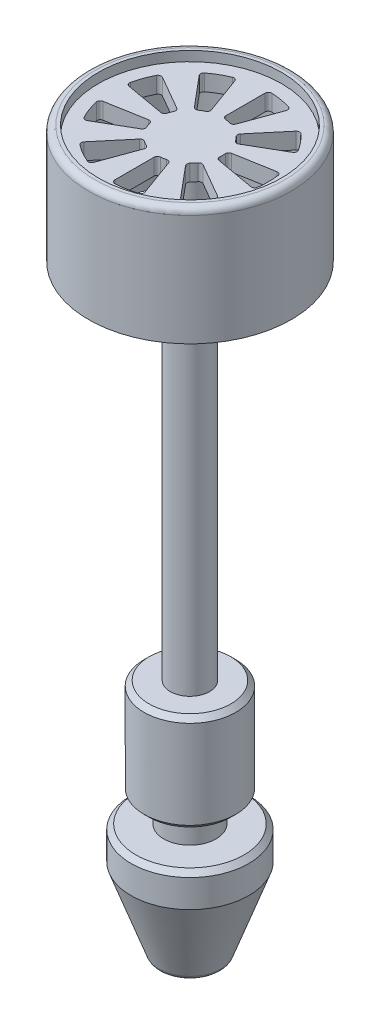
SolidWorks part; units mm, degrees
ref_plane "Alzado" through (0, 0, 0) normal (0, 0, 1) x (1, 0, 0)
ref_plane "Planta" through (0, 0, 0) normal (0, 1, 0) x (1, 0, 0)
ref_plane "Vista lateral" through (0, 0, 0) normal (1, 0, 0) x (0, 0, -1)
sketch "Croquis1" plane through (0, 0, 0) normal (0, 0, 1) x (1, 0, 0)
  line L0 (0, 0) -> (207.3621, 0) construction
  line L1 (0, 120) -> (239.3496, 120) construction
  line L2 (103.6811, 0) -> (103.6811, 171.5103) construction
  line L3 (97.6811, 120) -> (97.6811, 0)
  line L4 (97.6811, 0) -> (97.6811, -3.9826)
  line L5 (95.6811, -41.9826) -> (85.6811, -41.9826)
  line L6 (85.6811, -41.9826) -> (85.6811, -51.9826)
  line L7 (85.6811, -51.9826) -> (94.6811, -76.9826)
  line L8 (94.6811, -76.9826) -> (97.6811, -76.9826)
  line L9 (97.6811, -76.9826) -> (97.6811, -60.9826)
  line L10 (97.6811, -60.9826) -> (103.6811, -60.9826)
  line L11 (97.6811, 120) -> (97.6811, 135)
  line L12 (97.6811, 135) -> (75.6811, 135)
  line L13 (75.6811, 135) -> (75.6811, 107)
  line L14 (75.6811, 107) -> (72.6811, 107)
  line L15 (72.6811, 107) -> (72.6811, 143)
  line L16 (72.6811, 143) -> (75.6811, 143)
  line L17 (75.6811, 143) -> (75.6811, 140)
  line L18 (75.6811, 140) -> (103.6811, 140)
  line L19 (97.6811, -3.9826) -> (89.6811, -3.9826)
  line L20 (89.6811, -3.9826) -> (89.6811, -33.9826)
  line L21 (89.6811, -33.9826) -> (95.6811, -33.9826)
  line L22 (95.6811, -33.9826) -> (95.6811, -41.9826)
  line L23 (103.6811, -60.9826) -> (103.6811, 140)
  dimension "D4" = 56
  dimension "D10" = 14
  dimension "D1" = 120
  dimension "D2" = 12
  dimension "D3" = 207.3621
  dimension "D5" = 15
  dimension "D6" = 5
  dimension "D7" = 3
  dimension "D8" = 3
  dimension "D9" = 36
  dimension "D11" = 30
  dimension "D12" = 3.9826
  dimension "D13" = 8
  dimension "D14" = 18
  dimension "D15" = 10
  dimension "D16" = 8
  dimension "D17" = 35
  dimension "D18" = 16
  dimension "D19" = 6
  dimension "D20" = 3
revolve "Revolución1" add sketch "Croquis1" angle 360 about L23
fillet "Redondeo1" radius 2 1 edges at (103.6811, 143, -31)
chamfer "Chaflán1" distance 1.5 angle 45 3 edges at (103.6811, -41.9826, -18) (103.6811, -33.9826, -14) (103.6811, -3.9826, -14)
fillet "Redondeo2" radius 2 1 edges at (103.6811, -76.9826, -9)
sketch "Croquis2" plane through (0, 140, 0) normal (0, 1, 0) x (1, 0, 0)
  line L0 (103.6811, 10.9545) -> (103.6811, 22.9783)
  line L1 (107.4277, 10.2938) -> (111.5401, 21.5925)
  line L2 (110.7224, 8.3916) -> (118.4512, 17.6024)
  line L3 (113.1679, 5.4772) -> (123.5808, 11.4891)
  line L4 (114.4691, 1.9022) -> (126.3102, 3.9901)
  line L5 (114.4691, -1.9022) -> (126.3102, -3.9901)
  line L6 (113.1679, -5.4772) -> (123.5808, -11.4891)
  line L7 (110.7224, -8.3916) -> (118.4512, -17.6024)
  line L9 (103.6811, -10.9545) -> (103.6811, -22.9783)
  line L10 (99.9344, -10.2938) -> (95.822, -21.5925)
  line L11 (96.6397, -8.3916) -> (88.9109, -17.6024)
  line L12 (94.1942, -5.4772) -> (83.7813, -11.4891)
  line L13 (92.893, -1.9022) -> (81.0519, -3.9901)
  line L14 (92.893, 1.9022) -> (81.0519, 3.9901)
  line L15 (94.1942, 5.4772) -> (83.7813, 11.4891)
  line L16 (96.6397, 8.3916) -> (88.9109, 17.6024)
  line L17 (99.9344, 10.2938) -> (95.822, 21.5925)
  line L18 (107.4277, -10.2938) -> (111.5401, -21.5925)
  line L19 (100.2609, 9.3969) -> (103.6811, 0) [skipped]
  arc A0 (106.2328, 9.6689) -> (104.5902, 9.9586) centre (103.6811, 0) ccw
  arc A1 (110.9012, 22.8882) -> (104.7245, 23.9773) centre (103.6811, 0) ccw
  circle A2 centre (103.6811, 0) radius 24
  arc A3 (94.4998, 22.1744) -> (89.0681, 19.0384) centre (103.6811, 0) ccw
  arc A4 (111.8509, 5.7666) -> (110.7787, 7.0444) centre (103.6811, 0) ccw
  circle A5 centre (103.6811, 0) radius 10
  arc A6 (99.4208, 9.0471) -> (97.9762, 8.2131) centre (103.6811, 0) ccw
  arc A7 (123.9243, 12.8923) -> (119.8927, 17.6969) centre (103.6811, 0) ccw
  arc A8 (113.6462, -0.834) -> (113.6462, 0.834) centre (103.6811, 0) ccw
  arc A9 (127.4753, -3.136) -> (127.4753, 3.136) centre (103.6811, 0) ccw
  arc A10 (110.7787, -7.0444) -> (111.8509, -5.7666) centre (103.6811, 0) ccw
  arc A11 (119.8927, -17.6969) -> (123.9243, -12.8923) centre (103.6811, 0) ccw
  arc A12 (104.5902, -9.9586) -> (106.2328, -9.6689) centre (103.6811, 0) ccw
  arc A13 (104.7245, -23.9773) -> (110.9012, -22.8882) centre (103.6811, 0) ccw
  arc A14 (97.9762, -8.2131) -> (99.4208, -9.0471) centre (103.6811, 0) ccw
  arc A15 (89.0681, -19.0384) -> (94.4998, -22.1744) centre (103.6811, 0) ccw
  arc A16 (94.0316, -2.6246) -> (94.6021, -4.192) centre (103.6811, 0) ccw
  arc A17 (80.2492, -5.1912) -> (82.3944, -11.085) centre (103.6811, 0) ccw
  arc A18 (94.6021, 4.192) -> (94.0316, 2.6246) centre (103.6811, 0) ccw
  arc A19 (82.3944, 11.085) -> (80.2492, 5.1912) centre (103.6811, 0) ccw
  arc A20 (83.7813, 11.4891) -> (82.3944, 11.085) centre (83.2813, 10.6231) ccw
  arc A21 (94.1942, 5.4772) -> (94.6021, 4.192) centre (93.6942, 4.6112) cw
  arc A22 (94.0316, 2.6246) -> (92.893, 1.9022) centre (93.0667, 2.887) cw
  arc A23 (81.0519, 3.9901) -> (80.2492, 5.1912) centre (81.2256, 4.9749) cw
  arc A24 (81.0519, -3.9901) -> (80.2492, -5.1912) centre (81.2256, -4.9749) ccw
  arc A25 (83.7813, -11.4891) -> (82.3944, -11.085) centre (83.2813, -10.6231) cw
  arc A26 (92.893, -1.9022) -> (94.0316, -2.6246) centre (93.0667, -2.887) cw
  arc A27 (94.6021, -4.192) -> (94.1942, -5.4772) centre (93.6942, -4.6112) cw
  arc A28 (88.9109, -17.6024) -> (89.0681, -19.0384) centre (89.677, -18.2451) ccw
  arc A29 (96.6397, -8.3916) -> (97.9762, -8.2131) centre (97.4057, -9.0344) cw
  arc A30 (99.4208, -9.0471) -> (99.9344, -10.2938) centre (98.9947, -9.9518) cw
  arc A31 (95.822, -21.5925) -> (94.4998, -22.1744) centre (94.8823, -21.2505) cw
  arc A32 (106.2328, -9.6689) -> (107.4277, -10.2938) centre (106.488, -10.6358) cw
  arc A33 (103.6811, -10.9545) -> (104.5902, -9.9586) centre (104.6811, -10.9545) cw
  arc A34 (103.6811, -22.9783) -> (104.7245, -23.9773) centre (104.6811, -22.9783) ccw
  arc A35 (111.5401, -21.5925) -> (110.9012, -22.8882) centre (110.6004, -21.9345) cw
  arc A36 (118.4512, -17.6024) -> (119.8927, -17.6969) centre (119.2172, -16.9596) ccw
  arc A37 (123.5808, -11.4891) -> (123.9243, -12.8923) centre (123.0808, -12.3552) cw
  arc A38 (111.8509, -5.7666) -> (113.1679, -5.4772) centre (112.6679, -6.3433) cw
  arc A39 (110.7224, -8.3916) -> (110.7787, -7.0444) centre (111.4885, -7.7488) cw
  arc A40 (126.3102, -3.9901) -> (127.4753, -3.136) centre (126.4839, -3.0053) ccw
  arc A41 (126.3102, 3.9901) -> (127.4753, 3.136) centre (126.4839, 3.0053) cw
  arc A42 (113.6462, 0.834) -> (114.4691, 1.9022) centre (114.6427, 0.9174) cw
  arc A43 (114.4691, -1.9022) -> (113.6462, -0.834) centre (114.6427, -0.9174) cw
  arc A44 (118.4512, 17.6024) -> (119.8927, 17.6969) centre (119.2172, 16.9596) cw
  arc A45 (123.5808, 11.4891) -> (123.9243, 12.8923) centre (123.0808, 12.3552) ccw
  arc A46 (113.1679, 5.4772) -> (111.8509, 5.7666) centre (112.6679, 6.3433) cw
  arc A47 (110.7787, 7.0444) -> (110.7224, 8.3916) centre (111.4885, 7.7488) cw
  arc A48 (104.5902, 9.9586) -> (103.6811, 10.9545) centre (104.6811, 10.9545) cw
  arc A49 (107.4277, 10.2938) -> (106.2328, 9.6689) centre (106.488, 10.6358) cw
  arc A50 (111.5401, 21.5925) -> (110.9012, 22.8882) centre (110.6004, 21.9345) ccw
  arc A51 (103.6811, 22.9783) -> (104.7245, 23.9773) centre (104.6811, 22.9783) cw
  arc A52 (95.822, 21.5925) -> (94.4998, 22.1744) centre (94.8823, 21.2505) ccw
  arc A53 (88.9109, 17.6024) -> (89.0681, 19.0384) centre (89.677, 18.2451) cw
  arc A54 (99.4208, 9.0471) -> (99.9344, 10.2938) centre (98.9947, 9.9518) ccw
  arc A55 (97.9762, 8.2131) -> (96.6397, 8.3916) centre (97.4057, 9.0344) cw
  point P27 (103.6811, 0)
  point P46 (95.0208, 5)
  point P57 (93.833, -1.7365)
  point P64 (97.2532, -7.6604)
  point P73 (103.6811, -10)
  point P86 (110.1089, -7.6604)
  point P95 (113.5291, -1.7365)
  point P102 (112.3413, 5)
  point P109 (107.1013, 9.3969)
  point P114 (103.6811, 24)
  dimension "D4" = 1
  dimension "D3" = 18
  dimension "D1" = 4
  dimension "D2" = 4
extrude "Cortar-Extruir1" cut sketch "Croquis2" against normal up to next and the other way through all
